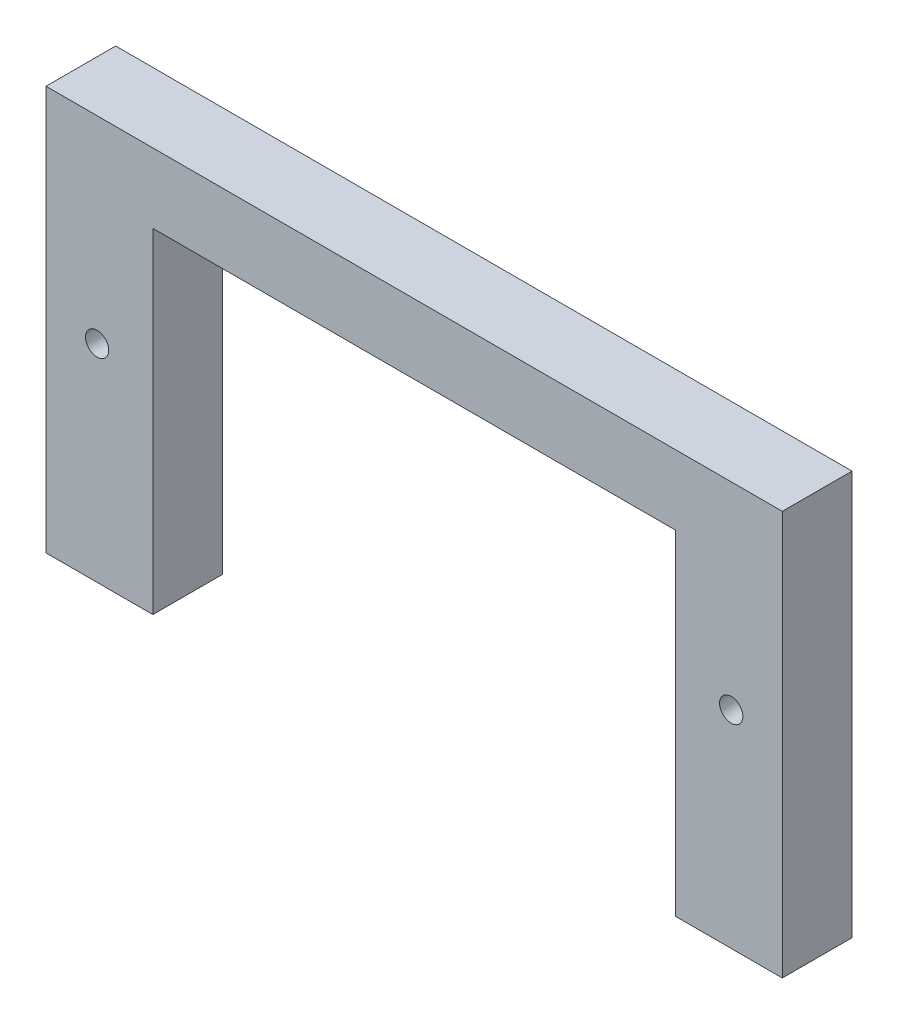
SolidWorks part; units mm, degrees
ref_plane "Front Plane" through (0, 0, 0) normal (0, 0, 1) x (1, 0, 0)
ref_plane "Top Plane" through (0, 0, 0) normal (0, 1, 0) x (1, 0, 0)
ref_plane "Right Plane" through (0, 0, 0) normal (1, 0, 0) x (0, 0, -1)
sketch "Sketch1" plane through (0, 0, 0) normal (0, 0, 1) x (1, 0, 0)
  line L0 (0, 0) -> (4.6, 0)
  line L1 (4.6, 0) -> (4.6, 14.4)
  line L2 (4.6, 14.4) -> (27.1, 14.4)
  line L3 (27.1, 14.4) -> (27.1, 0)
  line L4 (27.1, 0) -> (31.7, 0)
  line L5 (31.7, 0) -> (31.7, 17.4)
  line L6 (31.7, 17.4) -> (0, 17.4)
  line L7 (0, 17.4) -> (0, 0)
  circle A0 centre (29.5, 8.9) radius 0.5
  circle A1 centre (2.2, 8.9) radius 0.5
  dimension "D1" = 17.4
  dimension "D2" = 4.6
  dimension "D3" = 3
  dimension "D4" = 4.6
  dimension "D5" = 22.5
extrude "Boss-Extrude1" add sketch "Sketch1" along normal blind 3
